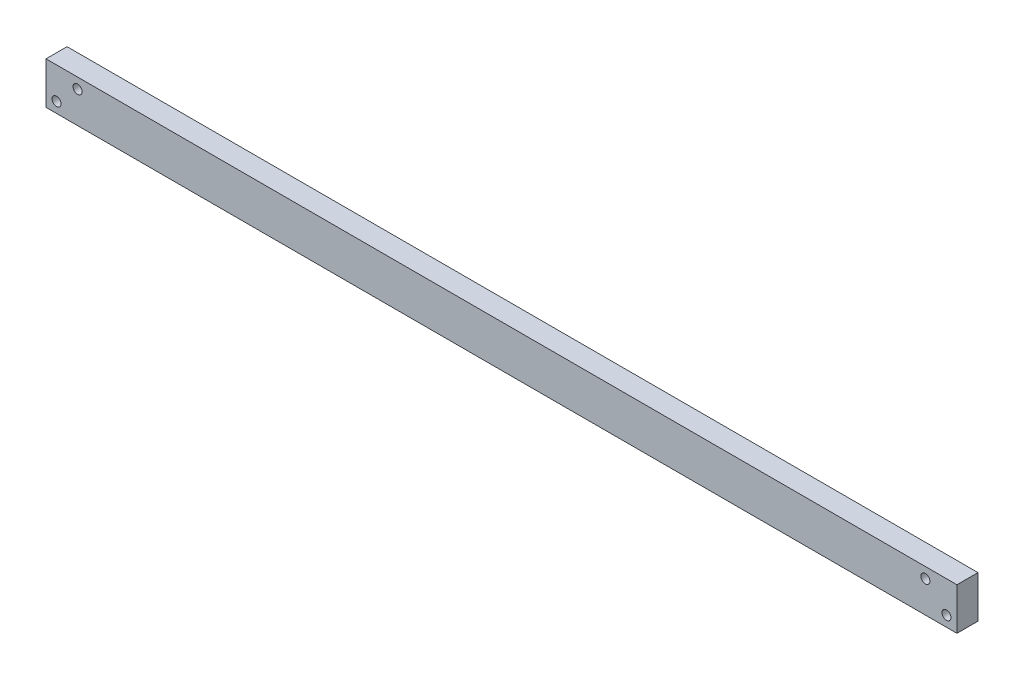
SolidWorks part; units mm, degrees
ref_plane "Ön Düzlem" through (0, 0, 0) normal (0, 0, 1) x (1, 0, 0)
ref_plane "Üst Düzlem" through (0, 0, 0) normal (0, 1, 0) x (1, 0, 0)
ref_plane "Sağ Düzlem" through (0, 0, 0) normal (1, 0, 0) x (0, 0, -1)
sketch "Çizim1" plane through (0, 0, 0) normal (0, 0, 1) x (1, 0, 0)
  line L1 (-303, -14) -> (303, -14)
  line L2 (-303, -14) -> (-303, 14)
  line L3 (-303, 14) -> (303, 14)
  line L4 (303, -14) -> (303, 14)
  line L5 (-303, -14) -> (303, 14) construction
  line L6 (-303, 14) -> (303, -14) construction
  point P0 (0, 0)
  dimension "D1" = 606
  dimension "D2" = 28
extrude "Yükseklik-Ekstrüzyon1" add sketch "Çizim1" along normal blind 14
sketch "Çizim2" plane through (0, 0, 14) normal (0, 0, 1) x (1, 0, 0)
  line L0 (-275, 14) -> (-275, -14) construction
  line L1 (-303, 14) -> (-303, -14) construction
  line L2 (303, 14) -> (-303, 14) construction
  line L3 (-296, 7) -> (-282, 7) construction
  line L4 (-296, 7) -> (-296, -7) construction
  line L5 (-296, -7) -> (-282, -7) construction
  line L6 (-282, 7) -> (-282, -7) construction
  line L7 (-296, 7) -> (-282, -7) construction
  line L8 (-296, -7) -> (-282, 7) construction
  line L9 (-303, -14) -> (303, -14) construction
  line L10 (-303, -14) -> (-275, -14) construction
  line L11 (0, 64.6485) -> (0, -64.6485) construction
  circle A0 centre (-282, 7) radius 3
  circle A1 centre (-296, -7) radius 3
  circle A2 centre (296, -7) radius 3
  circle A3 centre (282, 7) radius 3
  point P4 (-289, -14)
  point P8 (-289, 0)
  point P22 (-275, 0)
  dimension "D2" = 6
  dimension "D1" = 28
  dimension "D3" = 14
extrude "Kes-Ekstrüzyon1" cut sketch "Çizim2" against normal up to next
